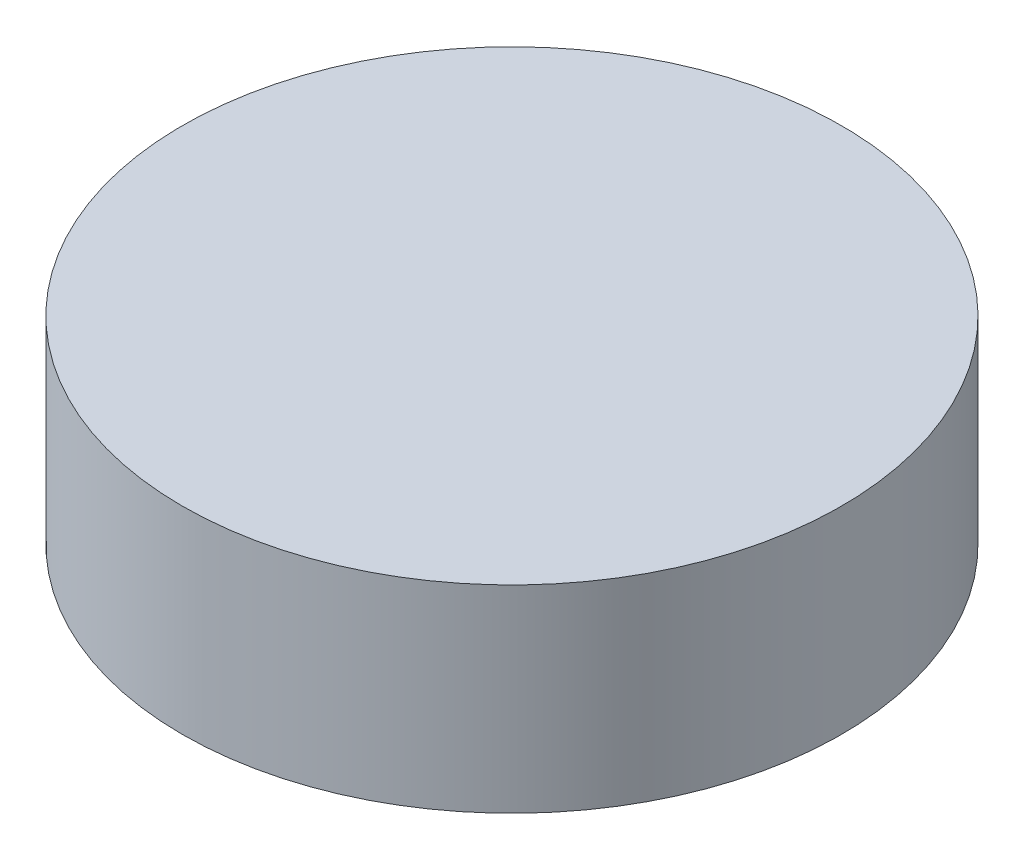
SolidWorks part; units mm, degrees
ref_plane "정면" through (0, 0, 0) normal (0, 0, 1) x (1, 0, 0)
ref_plane "윗면" through (0, 0, 0) normal (0, 1, 0) x (1, 0, 0)
ref_plane "우측면" through (0, 0, 0) normal (1, 0, 0) x (0, 0, -1)
sketch "스케치1" plane through (0, 0, 0) normal (0, 1, 0) x (1, 0, 0)
  circle A0 centre (-82.9083, 25.8094) radius 5
  dimension "D1" = 10
extrude "보스-돌출1" add sketch "스케치1" along normal blind 3
